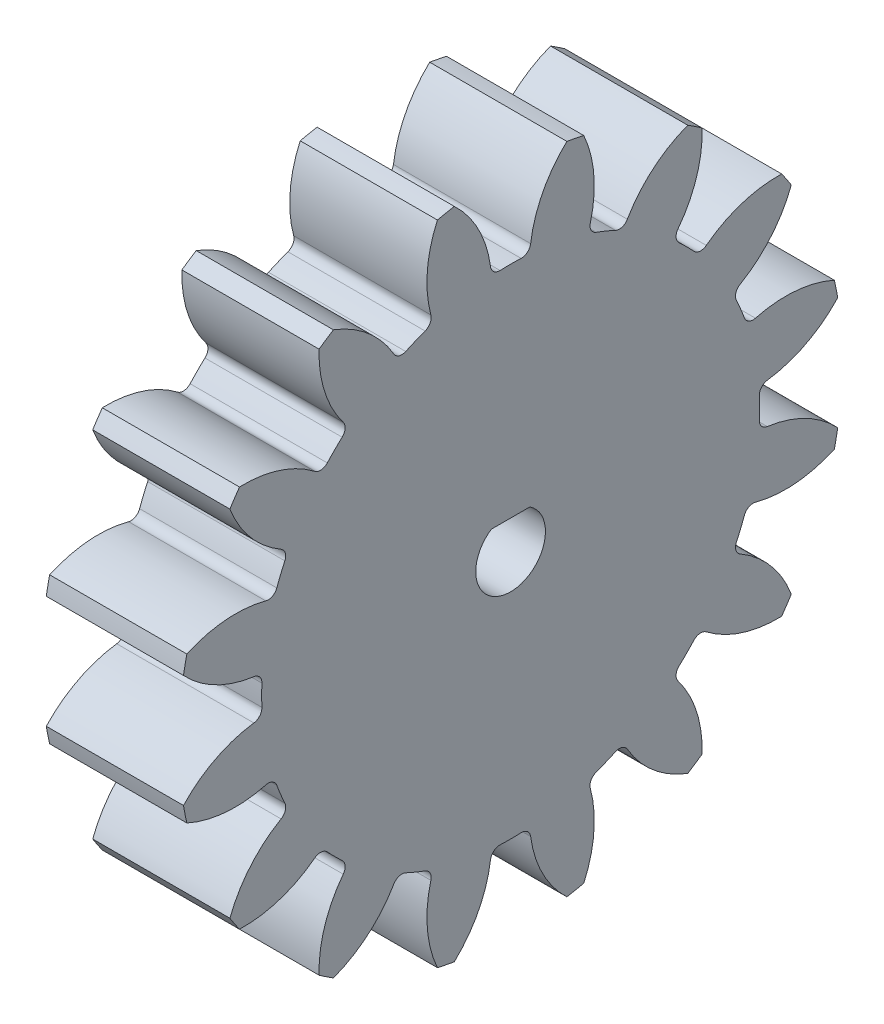
SolidWorks part; units mm, degrees
ref_plane "Plane1" through (0, 0, 0) normal (0, 0, 1) x (1, 0, 0)
ref_plane "Plane2" through (0, 0, 0) normal (0, 1, 0) x (1, 0, 0)
ref_plane "Plane3" through (0, 0, 0) normal (1, 0, 0) x (0, 0, -1)
sketch "HoldingSke" plane through (0, 0, 0) normal (0, 1, 0) x (1, 0, 0)
  line L0 (0, 0) -> (195.3284, -56.0095)
  line L1 (-15, 0) -> (100, 0) construction
  line L2 (0, 0) -> (-2.1039, 2.3779)
  line L3 (0, 0) -> (-11.863, 4.5341)
  line L4 (0, 0) -> (8.3015, 2.3804)
  line L5 (0, 0) -> (-47.5972, -17.7524)
  line L6 (0, 0) -> (-9.7909, -6.6059)
  line L7 (-2.1039, 2.3779) -> (8.8308, 51.9871)
  line L8 (-76.2, 54.61) -> (-75.184, 54.61)
  line L9 (-71.009, 38.7566) -> (-53.1078, 45.2721)
  line L10 (-76.2, 71.12) -> (104.1128, 71.12)
  line L11 (0, 0) -> (-11.811, 0)
  line L12 (-76.2, 101.6) -> (-76.0857, 101.6)
  line L13 (24.9733, 27.94) -> (52.9518, 28.4284)
  line L14 (24.9733, 27.94) -> (24.9746, 27.94)
  line L15 (24.9733, 27.94) -> (100.4006, 29.5858)
  circle A0 centre (0, 0) radius 0.3969
  circle A1 centre (0, 0) radius 21.43
  circle A2 centre (0, 0) radius 38.1
  circle A3 centre (0, 0) radius 0.3969
  dimension "MHD" = 42.86
  dimension "Hub_dia" = 76.2
  dimension "Bore" = 0.7937
  dimension "MBD" = 0.7937
  dimension "Num_teeth" = 16
  dimension "Pitch_radius" = 180.3128
  dimension "Pitch" = 203.2
  dimension "Width" = 11.811
  dimension "Overall_len" = 50.8
  dimension "Show_teeth" = 16
  dimension "Thickness" = 11.811
  dimension "OAL" = 50.8001
  dimension "T_dim" = 1.016
  dimension "Ap" = 20
  dimension "H" = 19.05
  dimension "Backlash" = 0.1143
  dimension "Addendum_fac" = 1
  dimension "Dedendum_fac" = 1.25
  dimension "Clearance_fac" = 0.25
  dimension "Dedendum_add" = 0.0013
sketch "BasProSke" plane through (0, 0, 0) normal (0, 1, 0) x (1, 0, 0)
  line L0 (-10, 0) -> (60, 0) construction
  line L1 (0, 0) -> (0, 28.575)
  line L2 (0, 0) -> (11.811, 0)
  line L3 (11.811, 0) -> (11.811, 28.575)
  line L4 (11.811, 28.575) -> (0, 28.575)
  dimension "Diameter" = 57.15
  dimension "Thickness" = 11.811
revolve "Base-Revolve" add sketch "BasProSke" angle 360 about L0
sketch "TooCutSke" plane through (0, 0, 0) normal (1, 0, 0) x (0, 0, -1)
  line L1 (0, 0) -> (0, 107) construction
  line L2 (0, 0) -> (-2.6895, 25.2572) construction
  line L3 (0, 0) -> (-9.8702, 49.6211) construction
  line L4 (-2.6895, 25.2572) -> (-4.9351, 24.8105) construction
  arc A0 (1.6538, 21.3661) -> (-1.6538, 21.3661) centre (0, 0) ccw
  arc A1 (4.8685, 28.183) -> (-4.8685, 28.183) centre (0, 0) ccw
  circle A2 centre (0, 0) radius 25.4 construction
  circle A3 centre (0, 0) radius 23.8682 construction
  arc A4 (-1.6538, 21.3661) -> (-4.8685, 28.183) centre (-11.7951, 20.7501) ccw
  arc A5 (4.8685, 28.183) -> (1.6538, 21.3661) centre (11.7951, 20.7501) ccw
  dimension "Root_dia" = 42.86
  dimension "Overcut_dia" = 57.2008
  dimension "Pitch_dia" = 50.8
  dimension "Base_dia" = 47.7364
  dimension "Flank_rad" = 10.16
  dimension "Half_ang" = 11.25
  dimension "Half_CT" = 2.2896
extrude "ToothCut" cut sketch "TooCutSke" along normal through all
fillet "Breaks" [suppressed] radius 0.0635
fillet "RootFillets" radius 0.795 2 edges at (5.9055, 21.3661, -1.6538) (5.9055, 21.3661, 1.6538)
pattern_circular "TeethCuts" count 16 every 22.5 about axis through (-10, 0, 0) along (1, 0, 0) of "ToothCut", "RootFillets", "Breaks"
sketch "HubNeaOneSke" plane through (0, 0, 0) normal (-1, 0, 0) x (0, 0, 1)
  circle A0 centre (0, 0) radius 21.43
  dimension "Diameter" = 42.86
extrude "HubNearOne" [suppressed] add sketch "HubNeaOneSke" along normal blind 38.9891
sketch "HubNeaBotSke" plane through (0, 0, 0) normal (-1, 0, 0) x (0, 0, 1)
  circle A0 centre (0, 0) radius 21.43
  dimension "Diameter" = 42.86
extrude "HubNearBoth" [suppressed] add sketch "HubNeaBotSke" along normal blind 19.4945
ref_plane "FarPln" through (11.811, 0, 0) normal (1, 0, 0) x (0, 0, -1)
sketch "HubFarSke" plane through (11.811, 0, 0) normal (1, 0, 0) x (0, 0, -1)
  circle A0 centre (0, 0) radius 21.43
  dimension "Diameter" = 42.86
extrude "HubFar" [suppressed] add sketch "HubFarSke" along normal blind 19.4945
sketch "BorSke" plane through (0, 0, 0) normal (1, 0, 0) x (0, 0, -1)
  circle A0 centre (0, 0) radius 0.3969
  dimension "Diameter" = 0.7937
extrude "Bore" cut sketch "BorSke" along normal mid plane 101.6001
sketch "KeySke" plane through (0, 0, 0) normal (1, 0, 0) x (0, 0, -1)
  line L0 (-0.127, 0) -> (-0.127, 0.6191)
  line L1 (-0.127, 0.6191) -> (0.127, 0.6191)
  line L2 (0.127, 0.6191) -> (0.127, 0)
  line L3 (0, 0) -> (0, 34) construction
  line L4 (-0.127, 0) -> (0.127, 0)
  dimension "Offset" = 0.6191
  dimension "Width" = 0.254
extrude "Keyway" [suppressed] cut sketch "KeySke" along normal mid plane 101.6001
pattern_circular "Keyway2" [suppressed] count 2 every 90 about axis through (-10, 0, 0) along (1, 0, 0)
sketch "Sketch1" plane through (11.811, 0, 0) normal (1, 0, 0) x (0, 0, -1)
  line L0 (-1.6583, 2.5) -> (1.6583, 2.5)
  arc A0 (-1.6583, 2.5) -> (1.6583, 2.5) centre (0, 0) ccw
  dimension "D1" = 6
  dimension "D2" = 2.5
extrude "Cut-Extrude1" cut sketch "Sketch1" against normal through all
equation "' \"Pitch@HoldingSke\" = 4"
equation "' \"Num_teeth@HoldingSke\" = 12"
equation "' \"Ap@HoldingSke\" =  20"
equation "' \"Width@HoldingSke\" = 0.5"
equation "' \"Hub_dia@HoldingSke\"= 1"
equation "' \"Overall_len@HoldingSke\" = 1.0"
equation "' \"Bore@HoldingSke\" = 0.75"
equation "' \"T_dim@HoldingSke\" = 0.85"
equation "' \"Width@KeySke\" = 0.25"
equation "' \"Show_teeth@HoldingSke\" = 13"
equation "' \"Backlash@HoldingSke\" = 0.009"
equation "' \"Addendum_fac@HoldingSke\" = 1.0"
equation "' \"Dedendum_fac@HoldingSke\" = 1.25"
equation "' \"Dedendum_add@HoldingSke\" = 0.00005"
equation "' \"Clearance_fac@HoldingSke\" = 0.25"
equation "' \"Pitch@HoldingSke\" = 0.5"
equation "' \"Num_teeth@HoldingSke\" = 23"
equation "' \"Show_teeth@HoldingSke\" = 23"
equation "' \"Backlash@HoldingSke\" = 0.0375"
equation "\"Overcut_dia@TooCutSke\" = (\"Num_teeth@HoldingSke\" + 2 * \"Addendum_fac@HoldingSke\") / \"Pitch@HoldingSke\" + 0.002"
equation "\"Pitch_dia@TooCutSke\" = \"Num_teeth@HoldingSke\" / \"Pitch@HoldingSke\""
equation "\"Base_dia@TooCutSke\" = \"Num_teeth@HoldingSke\" / \"Pitch@HoldingSke\" * cos((\"Ap@HoldingSke\"  * 3.14159265 / 180))"
equation "\"Root_dia@TooCutSke\" = (\"Num_teeth@HoldingSke\" + 2) / \"Pitch@HoldingSke\" - 2 * (\"Addendum_fac@HoldingSke\" + \"Dedendum_fac@HoldingSke\") / \"Pitch@HoldingSke\" - \"Dedendum_add@HoldingSke\" * 2"
equation "\"Half_ang@TooCutSke\" = 180 / \"Num_teeth@HoldingSke\""
equation "\"Half_CT@TooCutSke\" = \"Num_teeth@HoldingSke\" / \"Pitch@HoldingSke\" * sin((3.14159265 / 2 / \"Num_teeth@HoldingSke\")) / 2 - 7 * \"Backlash@HoldingSke\" / 4"
equation "\"Flank_rad@TooCutSke\" = \"Num_teeth@HoldingSke\" / \"Pitch@HoldingSke\" / 5"
equation "\"Radius@RootFillets\" = \"Clearance_fac@HoldingSke\" / \"Pitch@HoldingSke\" + \"Dedendum_add@HoldingSke\""
equation "\"Break_rad@Breaks\" = 0.02 / \"Pitch@HoldingSke\""
equation "\"Thickness@HoldingSke\" = \"Width@HoldingSke\""
equation "\"OAL@HoldingSke\" = \"Thickness@HoldingSke\""
equation "\"MHD@HoldingSke\" = (\"Num_teeth@HoldingSke\" + 2) / \"Pitch@HoldingSke\" - 2 * (\"Addendum_fac@HoldingSke\" + \"Dedendum_fac@HoldingSke\")  / \"Pitch@HoldingSke\" - \"Dedendum_add@HoldingSke\" * 2"
equation "\"MBD@HoldingSke\" = (\"Num_teeth@HoldingSke\" + 2) / \"Pitch@HoldingSke\" - 2 * (\"Addendum_fac@HoldingSke\" + \"Dedendum_fac@HoldingSke\")  / \"Pitch@HoldingSke\" - \"Dedendum_add@HoldingSke\" * 2 - 0.002"
equation "\"MHD@HoldingSke\" = ((sgn( \"MHD@HoldingSke\" - \"Hub_dia@HoldingSke\" )-1)*( \"MHD@HoldingSke\" - \"Hub_dia@HoldingSke\" ))/-2+ \"Hub_dia@HoldingSke\""
equation "\"MBD@HoldingSke\" = ((sgn( \"MBD@HoldingSke\" - \"Bore@HoldingSke\" )-1)*( \"MBD@HoldingSke\" - \"Bore@HoldingSke\" ))/-2+ \"Bore@HoldingSke\""
equation "\"OAL@HoldingSke\" = ((sgn( \"OAL@HoldingSke\" - \"Overall_len@HoldingSke\" )+1)*( \"OAL@HoldingSke\" - \"Overall_len@HoldingSke\" ))/2 + \"Overall_len@HoldingSke\" + 0.000002"
equation "\"Num_teeth@TeethCuts\" = int( \"Show_teeth@HoldingSke\" ) + 1"
equation "\"Num_teeth@TeethCuts\" = ((sgn( \"Num_teeth@TeethCuts\" - \"Num_teeth@HoldingSke\" )-1)*( \"Num_teeth@TeethCuts\" - \"Num_teeth@HoldingSke\" ))/-2+ \"Num_teeth@HoldingSke\""
equation "\"Num_teeth@TeethCuts\" = ((sgn( \"Num_teeth@TeethCuts\" - 2.0)+1)*( \"Num_teeth@TeethCuts\" - 2.0))/2 +2.0"
equation "\"Angle@TeethCuts\" = 360.0 / \"Num_teeth@HoldingSke\""
equation "\"Diameter@BasProSke\" = (\"Num_teeth@HoldingSke\" + 2 * \"Addendum_fac@HoldingSke\") / \"Pitch@HoldingSke\""
equation "\"Thickness@BasProSke\"  = \"Thickness@HoldingSke\""
equation "' \"Fillet_rad@BasProSke\" =  \"Thickness@HoldingSke\" * 0.05"
equation "\"MHD@HoldingSke\" = ((sgn( \"MHD@HoldingSke\" - \"Root_dia@TooCutSke\" )-1)*( \"MHD@HoldingSke\" - \"Root_dia@TooCutSke\" ))/-2+ \"Root_dia@TooCutSke\""
equation "\"Diameter@HubNeaOneSke\" = \"MHD@HoldingSke\""
equation "\"Length@HubNearOne\" = \"OAL@HoldingSke\" - \"Thickness@BasProSke\""
equation "\"Diameter@HubNeaBotSke\" = \"MHD@HoldingSke\""
equation "\"Length@HubNearBoth\" = ( \"OAL@HoldingSke\" - \"Thickness@BasProSke\" ) / 2.0"
equation "\"Thickness@FarPln\" = \"Thickness@BasProSke\""
equation "\"Diameter@HubFarSke\" = \"MHD@HoldingSke\""
equation "\"Length@HubFar\" = ( \"OAL@HoldingSke\" - \"Thickness@BasProSke\" ) / 2.0"
equation "\"Diameter@BorSke\" = \"MBD@HoldingSke\""
equation "\"D1@Bore\" = \"OAL@HoldingSke\" * 2.0"
equation "\"D1@Keyway\" = \"OAL@HoldingSke\" * 2.0"
equation "\"Offset@KeySke\" = \"T_dim@HoldingSke\" - \"MBD@HoldingSke\" / 2.0"
